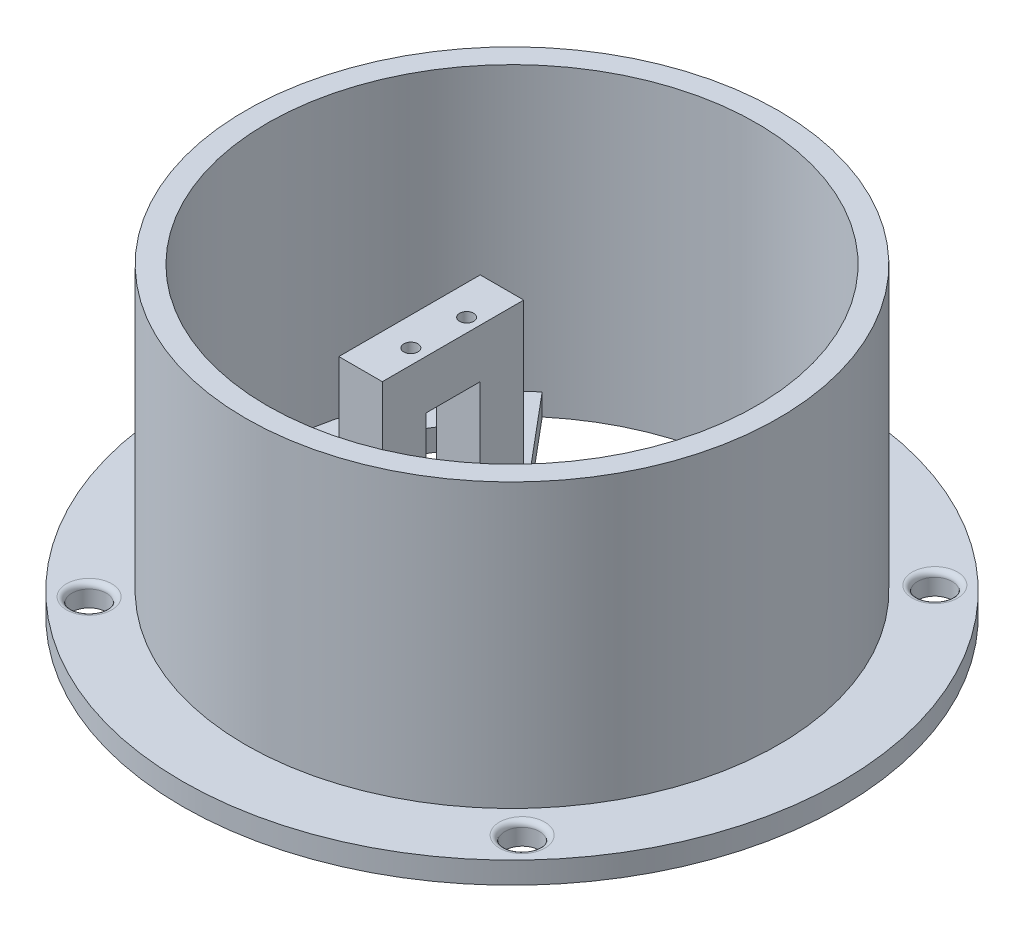
SolidWorks part; units mm, degrees
ref_plane "Alzado" through (0, 0, 0) normal (0, 0, 1) x (1, 0, 0)
ref_plane "Planta" through (0, 0, 0) normal (0, 1, 0) x (1, 0, 0)
ref_plane "Vista lateral" through (0, 0, 0) normal (1, 0, 0) x (0, 0, -1)
sketch "Croquis1" plane through (0, 0, 0) normal (0, 1, 0) x (1, 0, 0)
  line L0 (-11.25, 13.4072) -> (-11.25, -12.5928)
  line L7 (-11.25, 13.4072) -> (-28.9254, 34.472)
  line L8 (-11.25, -12.5928) -> (-29.3245, -34.1332)
  arc A2 (-28.9254, 34.472) -> (-29.3245, -34.1332) centre (0, 0) ccw
  point P4 (-15.245, 0)
  point P6 (-11.25, 0.4072)
  dimension "D1" = 11.25
  dimension "D2" = 90
  dimension "D5" = 26
extrude "Saliente-Extruir2" add sketch "Croquis1" along normal blind 4
sketch "Croquis4" plane through (0, 4, 0) normal (0, 1, 0) x (1, 0, 0)
  line L0 (-11.25, 13.4072) -> (-11.25, -12.5928)
  line L1 (-11.25, -12.5928) -> (-19.25, -12.5928)
  line L2 (-19.25, -12.5928) -> (-19.25, 13.4072)
  line L3 (-19.25, 13.4072) -> (-11.25, 13.4072)
  dimension "D1" = 8
extrude "Saliente-Extruir4" add sketch "Croquis4" along normal blind 34
sketch "Croquis5" plane through (-11.25, 0, 0) normal (1, 0, 0) x (0, 0, -1)
  line L0 (-12.5928, 38) -> (13.4072, 38) construction
  line L1 (-4.5928, 29) -> (5.4072, 29)
  line L2 (-4.5928, 29) -> (-4.5928, 5)
  line L3 (-4.5928, 5) -> (5.4072, 5)
  line L4 (5.4072, 29) -> (5.4072, 5)
  line L5 (-4.5928, 29) -> (5.4072, 5) construction
  line L6 (-4.5928, 5) -> (5.4072, 29) construction
  line L7 (-12.5928, 38) -> (-12.5928, 4) construction
  line L8 (-12.5928, 0) -> (13.4072, 0) construction
  line L9 (13.4072, 38) -> (13.4072, 4) construction
  point P0 (0.4072, 17)
  dimension "D1" = 9
  dimension "D2" = 8
  dimension "D3" = 5
  dimension "D4" = 8
extrude "Cortar-Extruir1" cut sketch "Croquis5" against normal up to next
sketch "Croquis6" plane through (0, 38, 0) normal (0, 1, 0) x (1, 0, 0)
  line L0 (-11.25, 13.4072) -> (-19.25, 13.4072) construction
  line L1 (-19.25, 13.4072) -> (-19.25, -12.5928) construction
  circle A0 centre (-13.75, 5.4072) radius 1.3
  circle A1 centre (-14.0093, -4.5928) radius 1.3
  dimension "D1" = 2.6
  dimension "D2" = 8
  dimension "D3" = 5.5
  dimension "D4" = 10
extrude "Cortar-Extruir2" cut sketch "Croquis6" against normal blind 7
sketch "Croquis8" plane through (0, 0, 0) normal (0, 1, 0) x (1, 0, 0)
  line L0 (31.75, 13.4072) -> (31.75, -12.6178)
  line L1 (31.75, 13.4072) -> (43.05, 13.4072)
  line L2 (31.75, -12.6178) -> (43.288, -12.6178)
  arc A0 (43.288, -12.6178) -> (43.05, 13.4072) centre (0, 0) ccw
  dimension "D1" = 11.3
  dimension "D2" = 31.75
extrude "Saliente-Extruir5" add sketch "Croquis8" along normal blind 38 separate body
sketch "Croquis10" plane through (0, 0, 0) normal (0, 1, 0) x (1, 0, 0)
  circle A0 centre (0, 0) radius 45
  circle A1 centre (0, 0) radius 49
  dimension "D1" = 98
extrude "Saliente-Extruir6" add sketch "Croquis10" along normal blind 56
sketch "Croquis11" plane through (0, 4, 0) normal (0, 1, 0) x (1, 0, 0)
  line L0 (-24.25, 17.1369) -> (-24.25, -15.0431)
  line L1 (-19.25, 13.4072) -> (-19.25, -12.5928) construction
  line L2 (-24.25, 17.1369) -> (-29.4777, 23.4024)
  line L3 (-24.25, -15.0431) -> (-29.4777, -21.3087)
  arc A1 (-29.4777, 23.4024) -> (-29.4777, -21.3087) centre (-7.1121, 1.0469) ccw
  dimension "D1" = 32.18
  dimension "D2" = 5
  dimension "D3" = 8.16
  dimension "D4" = 8.16
extrude "Cortar-Extruir3" cut sketch "Croquis11" against normal blind 38
sketch "Croquis12" plane through (0, 0, 0) normal (0, 1, 0) x (1, 0, 0)
  circle A0 centre (0, 0) radius 60.625
  circle A1 centre (0, 0) radius 49
  dimension "D1" = 121.25
extrude "Saliente-Extruir8" add sketch "Croquis12" along normal blind 4
sketch "Croquis13" plane through (0, 0, 0) normal (0, 1, 0) x (1, 0, 0)
  circle A0 centre (-39.8155, 37.9466) radius 3.1645
  circle A1 centre (37.9445, 39.8147) radius 3.1645
  circle A2 centre (39.814, -37.9453) radius 3.1645
  circle A3 centre (-37.946, -39.8134) radius 3.1645
  dimension "D1" = 6.329
  dimension "D2" = 55.002
  dimension "D3" = 77.76
  dimension "D4" = 55
  dimension "D5" = 77.76
  dimension "D6" = 77.76
  dimension "D7" = 55
  dimension "D8" = 55
  dimension "D9" = 77.76
extrude "Cortar-Extruir5" cut sketch "Croquis13" along normal blind 14
sketch "Croquis14" plane through (0, 38, 0) normal (0, 1, 0) x (1, 0, 0)
  line L0 (31.75, 13.4072) -> (39.75, 13.4072)
  line L1 (42.9563, 13.4072) -> (31.75, 13.4072) construction
  line L2 (31.75, -12.6178) -> (39.75, -12.6178)
  line L3 (31.75, -12.6178) -> (43.1948, -12.6178) construction
  line L5 (39.75, 13.4072) -> (39.75, -12.6178)
  circle A0 centre (34.25, 5.4072) radius 1.3
  circle A1 centre (34.25, -4.6178) radius 1.3
  dimension "D1" = 2.6
  dimension "D6" = 2.6
  dimension "D2" = 8
  dimension "D3" = 8
  dimension "D4" = 8
  dimension "D5" = 5.5
  dimension "D7" = 8
  dimension "D8" = 5.5
extrude "Cortar-Extruir6" cut sketch "Croquis14" against normal blind 5 contours A0 | A1
fillet "Redondeo1" radius 1 4 edges at (-39.8155, 4, -34.7821) (37.9445, 4, -36.6502) (39.814, 4, 41.1098) (-37.946, 4, 42.9779)
